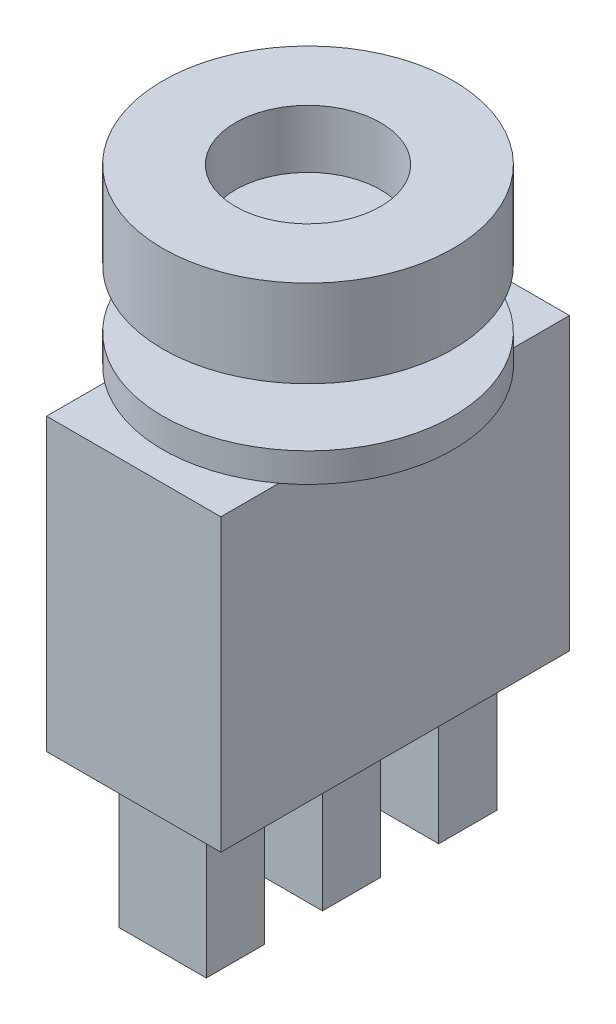
SolidWorks part; units mm, degrees
ref_plane "Plan de face" through (0, 0, 0) normal (0, 0, 1) x (1, 0, 0)
ref_plane "Plan de dessus" through (0, 0, 0) normal (0, 1, 0) x (1, 0, 0)
ref_plane "Plan de droite" through (0, 0, 0) normal (1, 0, 0) x (0, 0, -1)
sketch "Esquisse1" plane through (0, 0, 0) normal (0, 1, 0) x (1, 0, 0)
  circle A0 centre (0, 0) radius 5
  dimension "D1" = 10
extrude "Extrusion1" add sketch "Esquisse1" along normal blind 3
sketch "Esquisse3" plane through (0, 0, 0) normal (0, -1, 0) x (1, 0, 0)
  circle A0 centre (0, 0) radius 2
  dimension "D1" = 4
extrude "Extrusion3" add sketch "Esquisse3" along normal blind 2
sketch "Esquisse4" plane through (0, -2, 0) normal (0, -1, 0) x (1, 0, 0)
  circle A0 centre (0, 0) radius 5
  dimension "D1" = 10
extrude "Extrusion4" add sketch "Esquisse4" along normal blind 1
sketch "Esquisse5" plane through (0, -3, 0) normal (0, -1, 0) x (1, 0, 0)
  line L0 (0, 0) -> (0, 3.7815) construction
  line L1 (3, -6) -> (-3, -6)
  line L2 (3, -6) -> (3, 6)
  line L3 (3, 6) -> (-3, 6)
  line L4 (-3, -6) -> (-3, 6)
  line L5 (-1.6151, 0) -> (1.2087, 0) construction
  dimension "D1" = 6
  dimension "D2" = 3
  dimension "D3" = 6
  dimension "D4" = 12
extrude "Extrusion5" add sketch "Esquisse5" along normal blind 10
sketch "Esquisse6" plane through (0, -13, 0) normal (0, -1, 0) x (1, 0, 0)
  line L0 (0, 8.662) -> (0, -8.4735) construction
  line L1 (-1.5, 3) -> (1.5, 3)
  line L2 (-1.5, 3) -> (-1.5, 5)
  line L3 (-1.5, 5) -> (1.5, 5)
  line L4 (1.5, 3) -> (1.5, 5)
  line L5 (-1.5, -1) -> (1.5, -1)
  line L6 (-1.5, -1) -> (-1.5, 1)
  line L7 (-1.5, 1) -> (1.5, 1)
  line L8 (1.5, -1) -> (1.5, 1)
  line L9 (-1.5, -5) -> (1.5, -5)
  line L10 (-1.5, -5) -> (-1.5, -3)
  line L11 (-1.5, -3) -> (1.5, -3)
  line L12 (1.5, -5) -> (1.5, -3)
  line L13 (-5.4044, 0) -> (7.318, 0) construction
  dimension "D1" = 3
  dimension "D2" = 2
  dimension "D3" = 2
  dimension "D4" = 2
  dimension "D5" = 1
  dimension "D6" = 1.5
  dimension "D7" = 1.5
  dimension "D8" = 1.5
extrude "Extrusion6" add sketch "Esquisse6" along normal blind 5
sketch "Esquisse2" plane through (0, 3, 0) normal (0, 1, 0) x (-1, 0, 0)
  circle A0 centre (0, 0) radius 2.5
  dimension "D1" = 5
extrude "Extrusion7" cut sketch "Esquisse2" against normal blind 2
